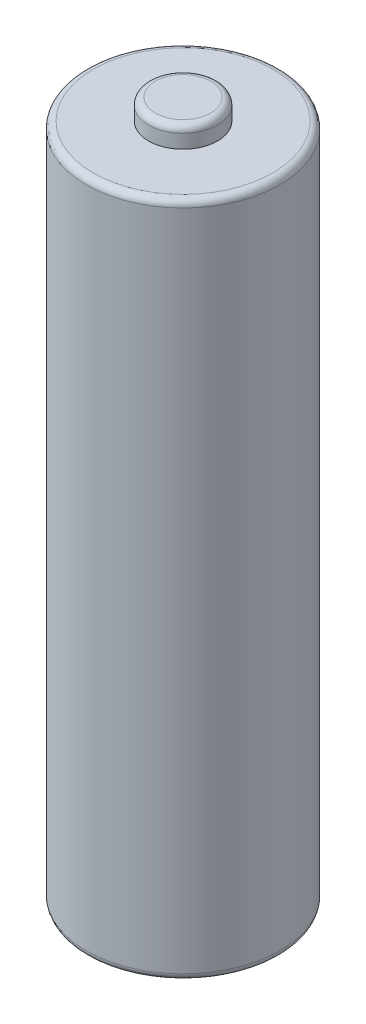
SolidWorks part; units mm, degrees
ref_plane "Front Plane" through (0, 0, 0) normal (0, 0, 1) x (1, 0, 0)
ref_plane "Top Plane" through (0, 0, 0) normal (0, 1, 0) x (1, 0, 0)
ref_plane "Right Plane" through (0, 0, 0) normal (1, 0, 0) x (0, 0, -1)
sketch "Sketch1" plane through (0, 0, 0) normal (0, 1, 0) x (1, 0, 0)
  circle A0 centre (0, 0) radius 7
  dimension "D1" = 14
extrude "Boss-Extrude1" add sketch "Sketch1" along normal blind 49
sketch "Sketch2" plane through (0, 49, 0) normal (0, 1, 0) x (1, 0, 0)
  circle A0 centre (0, 0) radius 2.5
  dimension "D1" = 5
extrude "Boss-Extrude2" add sketch "Sketch2" along normal blind 1.5
fillet "Fillet1" radius 0.5 3 edges at (0, 0, 7) (0, 50.5, 2.5) (0, 49, 7)
